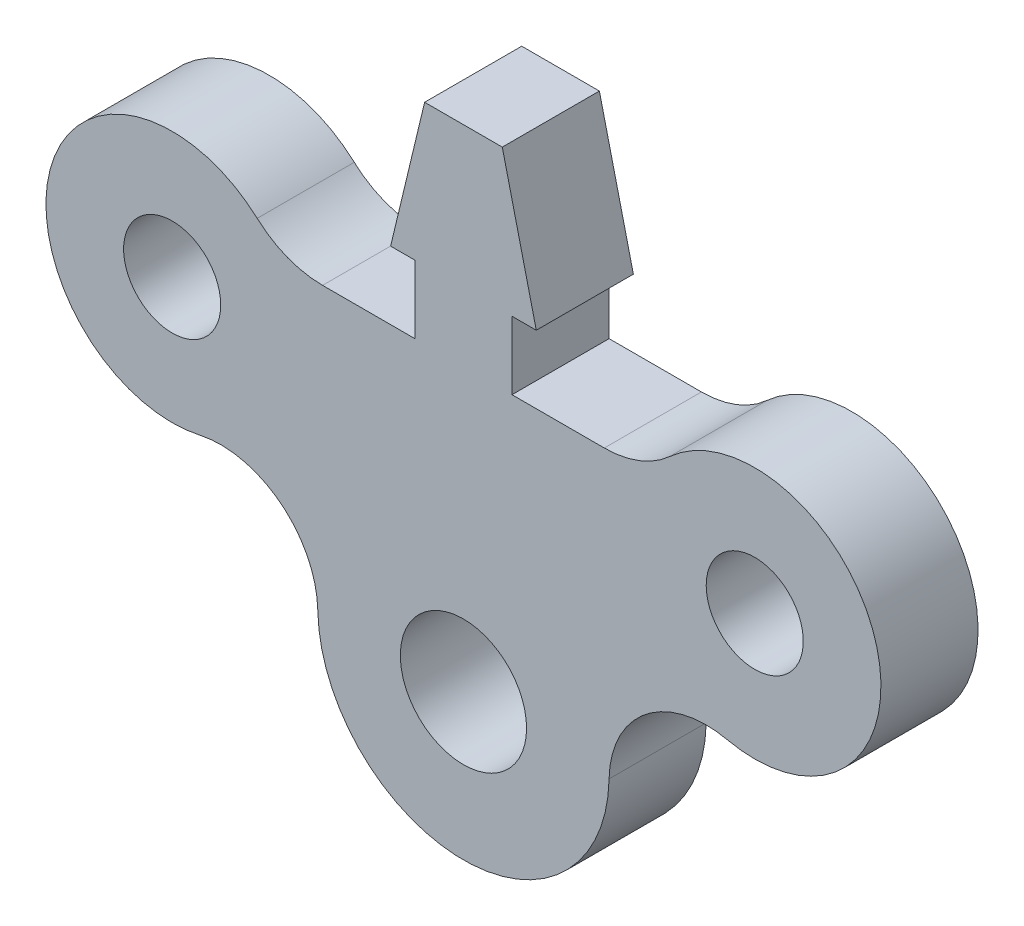
SolidWorks part; units mm, degrees
ref_plane "Ön Düzlem" through (0, 0, 0) normal (0, 0, 1) x (1, 0, 0)
ref_plane "Üst Düzlem" through (0, 0, 0) normal (0, 1, 0) x (1, 0, 0)
ref_plane "Sağ Düzlem" through (0, 0, 0) normal (1, 0, 0) x (0, 0, -1)
sketch "Sketch1" plane through (0, 0, 0) normal (0, 0, 1) x (1, 0, 0)
  line L0 (14.452, 10.1066) -> (4.944, 10.1066)
  line L1 (14.452, 10.1066) -> (14.452, 17.1066)
  line L2 (14.452, 17.1066) -> (11.952, 17.1066)
  line L3 (11.952, 17.1066) -> (15.4528, 31.6924)
  line L5 (15.4528, 31.6924) -> (19.452, 31.6924)
  line L8 (23.4513, 31.6924) -> (19.452, 31.6924)
  line L9 (26.952, 17.1066) -> (23.4513, 31.6924)
  line L10 (24.452, 17.1066) -> (26.952, 17.1066)
  line L11 (24.452, 10.1066) -> (33.9601, 10.1066)
  line L12 (24.452, 10.1066) -> (24.452, 17.1066)
  circle A0 centre (-10.548, 3.1066) radius 5
  arc A1 (-1.7916, 12.7153) -> (-7.7196, -9.582) centre (-10.548, 3.1066) ccw
  arc A2 (4.944, 10.1066) -> (-1.7916, 12.7153) centre (4.944, 20.1066) cw
  arc A5 (33.9601, 10.1066) -> (40.6957, 12.7153) centre (33.9601, 20.1066) ccw
  arc A6 (40.6957, 12.7153) -> (46.6237, -9.582) centre (49.452, 3.1066) cw
  circle A7 centre (49.452, 3.1066) radius 5
  circle A9 centre (19.452, -18.8934) radius 6.5
  arc A11 (4.4545, -19.1628) -> (34.4496, -19.1628) centre (19.452, -18.8934) ccw
  arc A12 (-7.7196, -9.582) -> (4.4545, -19.1628) centre (-5.5439, -19.3425) cw
  arc A13 (46.6237, -9.582) -> (34.4496, -19.1628) centre (44.448, -19.3425) ccw
  point P10 (0, 0)
  point P14 (0, 0)
  dimension "D1" = 10
  dimension "D2" = 26
  dimension "D3" = 10
  dimension "D11" = 30
  dimension "D12" = 13
  dimension "D13" = 10
  dimension "D14" = 10
  dimension "D15" = 60
  dimension "D4" = 7
  dimension "D5" = 7
  dimension "D6" = 15
  dimension "D7" = 7.9985
  dimension "D8" = 15
  dimension "D9" = 10
  dimension "D10" = 22
extrude "Boss-Extrude1" add sketch "Sketch1" along normal blind 10
